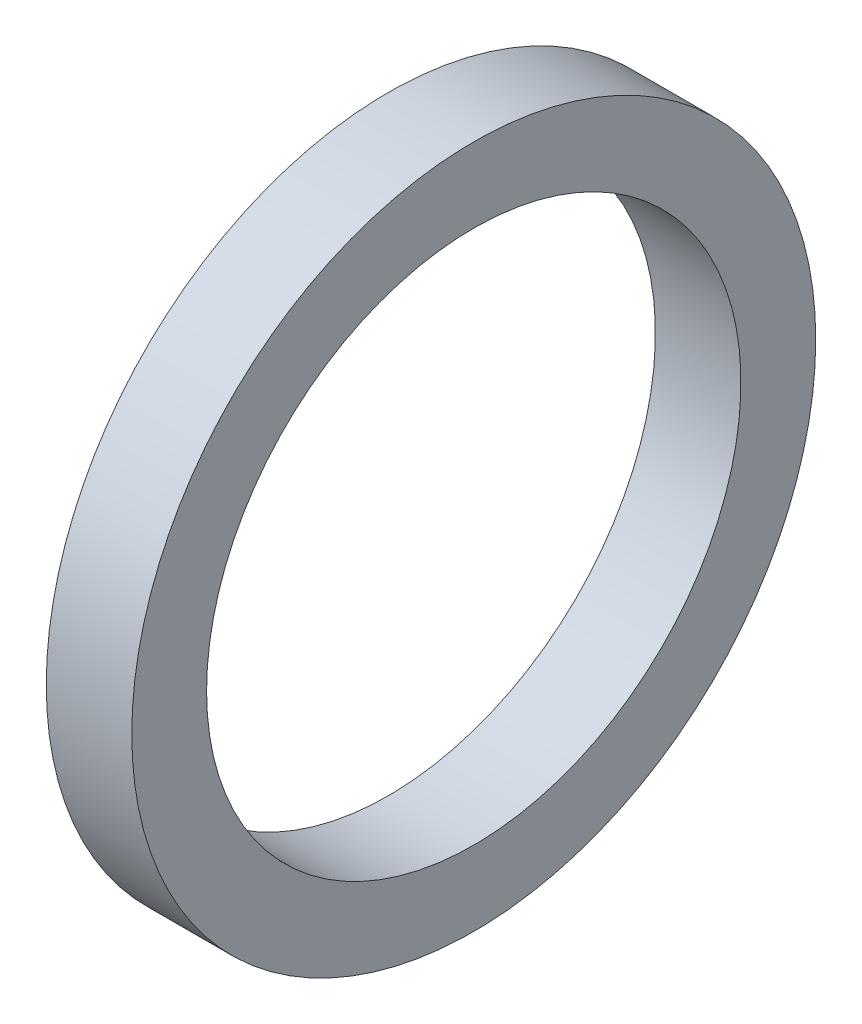
SolidWorks part; units mm, degrees
material "Alloy Steel"
ref_plane "Front Plane" through (0, 0, 0) normal (0, 0, 1) x (1, 0, 0)
ref_plane "Top Plane" through (0, 0, 0) normal (0, 1, 0) x (1, 0, 0)
ref_plane "Right Plane" through (0, 0, 0) normal (1, 0, 0) x (0, 0, -1)
sketch "Sketch1" plane through (0, 0, 0) normal (0, 0, 1) x (1, 0, 0)
  line L0 (0, 0) -> (10.7093, 0) construction
  line L1 (-2, 16) -> (2, 16)
  line L2 (-2, 16) -> (-2, 12.5)
  line L3 (-2, 12.5) -> (2, 12.5)
  line L4 (2, 16) -> (2, 12.5)
  line L5 (-2, 16) -> (2, 12.5) construction
  line L6 (-2, 12.5) -> (2, 16) construction
  point P0 (0, 14.25)
  point P8 (0, 0)
  dimension "D1" = 25
  dimension "D2" = 32
  dimension "D3" = 4
revolve "Revolve1" add sketch "Sketch1" angle 360 about L0
